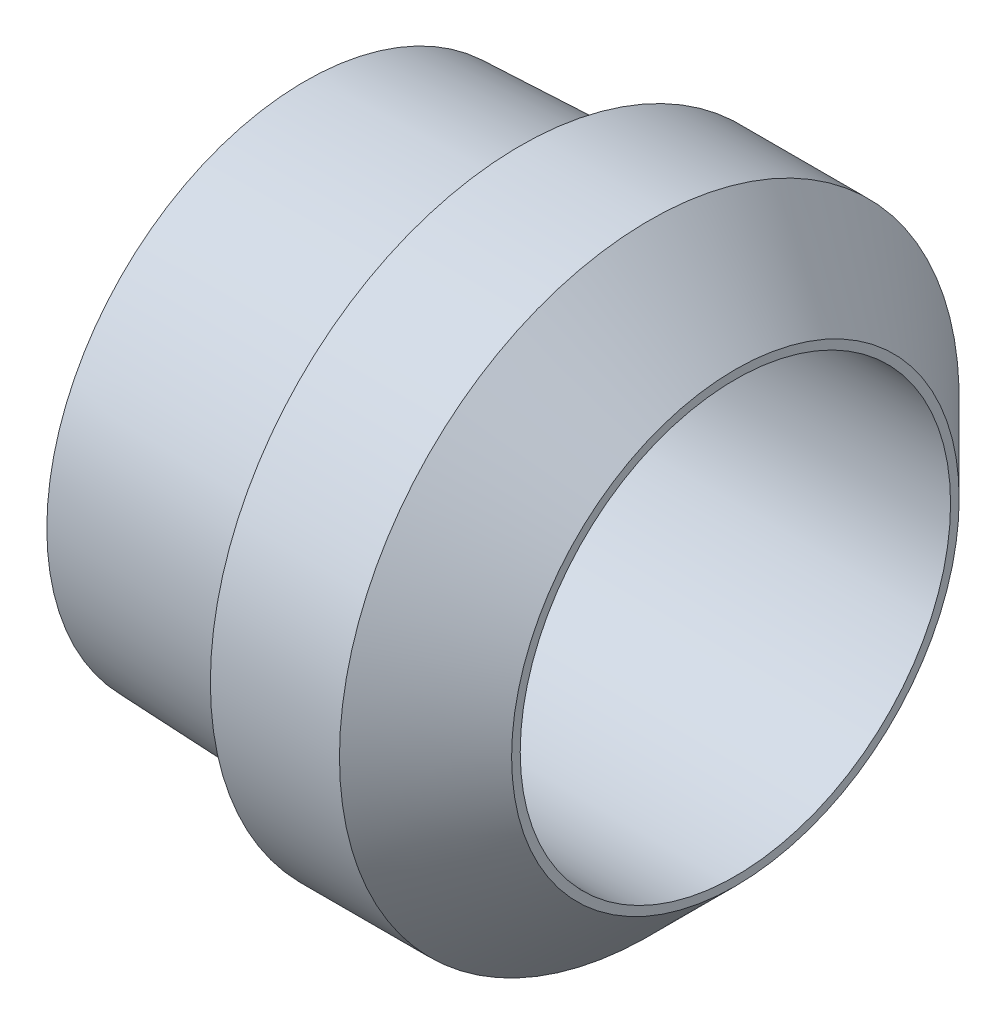
SolidWorks part; units mm, degrees
ref_plane "Plane1" through (0, 0, 0) normal (0, 0, 1) x (1, 0, 0)
ref_plane "Plane2" through (0, 0, 0) normal (0, 1, 0) x (1, 0, 0)
ref_plane "Plane3" through (0, 0, 0) normal (1, 0, 0) x (0, 0, -1)
sketch "Sketch1" plane through (0, 0, 0) normal (0, 0, 1) x (1, 0, 0)
  line L0 (-12, 0) -> (84, 0) construction
  line L1 (0, 5) -> (0, 6)
  line L2 (0, 6) -> (5, 6.2)
  line L3 (5, 6.2) -> (5, 7.2)
  line L4 (5, 7.2) -> (8, 7.2)
  line L5 (8, 7.2) -> (10, 5.2)
  line L6 (10, 5.2) -> (10, 5)
  line L7 (10, 5) -> (0, 5)
  dimension "Indv. dia." = 10
  dimension "D2" = 1
  dimension "D3" = 1
  dimension "Dia. ved kant" = 12.4
  dimension "D5" = 2
  dimension "D6" = 45
  dimension "Længde2" = 5
  dimension "Længde1" = 10
revolve "Base-Revolve" add sketch "Sketch1" angle 360 about L0
